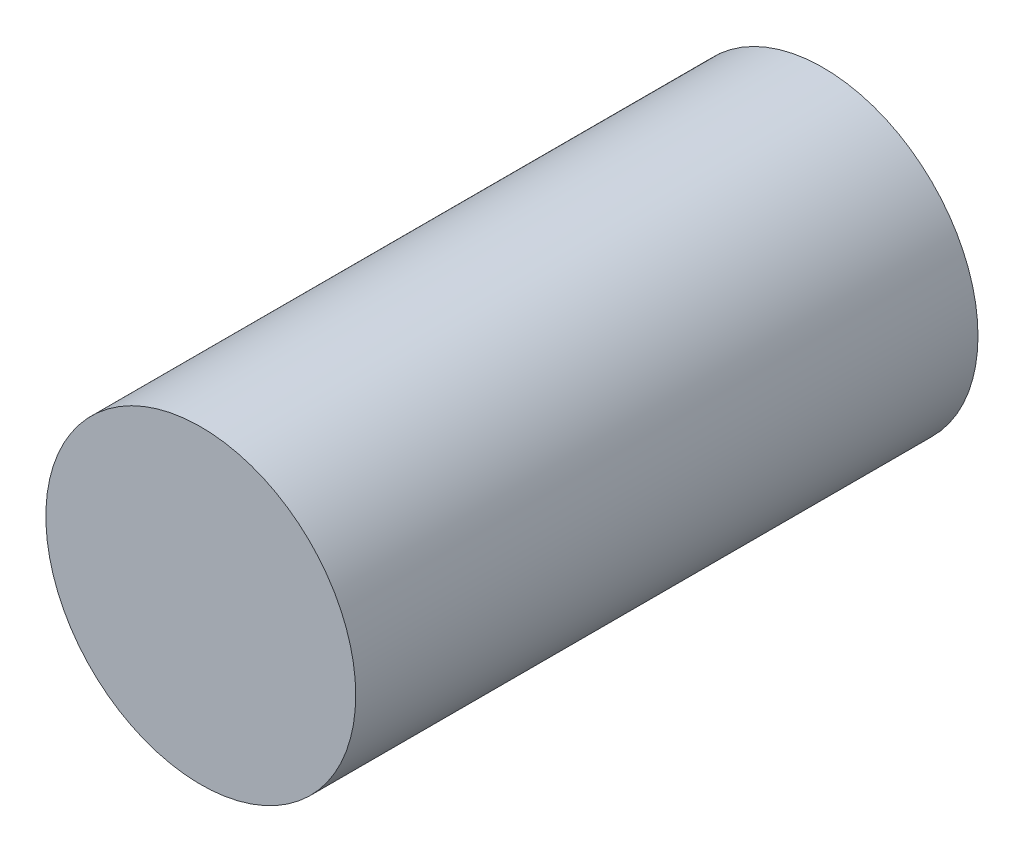
SolidWorks part; units mm, degrees
ref_plane "Front Plane" through (0, 0, 0) normal (0, 0, 1) x (1, 0, 0)
ref_plane "Top Plane" through (0, 0, 0) normal (0, 1, 0) x (1, 0, 0)
ref_plane "Right Plane" through (0, 0, 0) normal (1, 0, 0) x (0, 0, -1)
sketch "Sketch1" plane through (0, 0, 0) normal (0, 0, 1) x (1, 0, 0)
  circle A0 centre (0, 0) radius 2.49
  dimension "D1" = 4.98
extrude "Boss-Extrude1" add sketch "Sketch1" along normal blind 10
